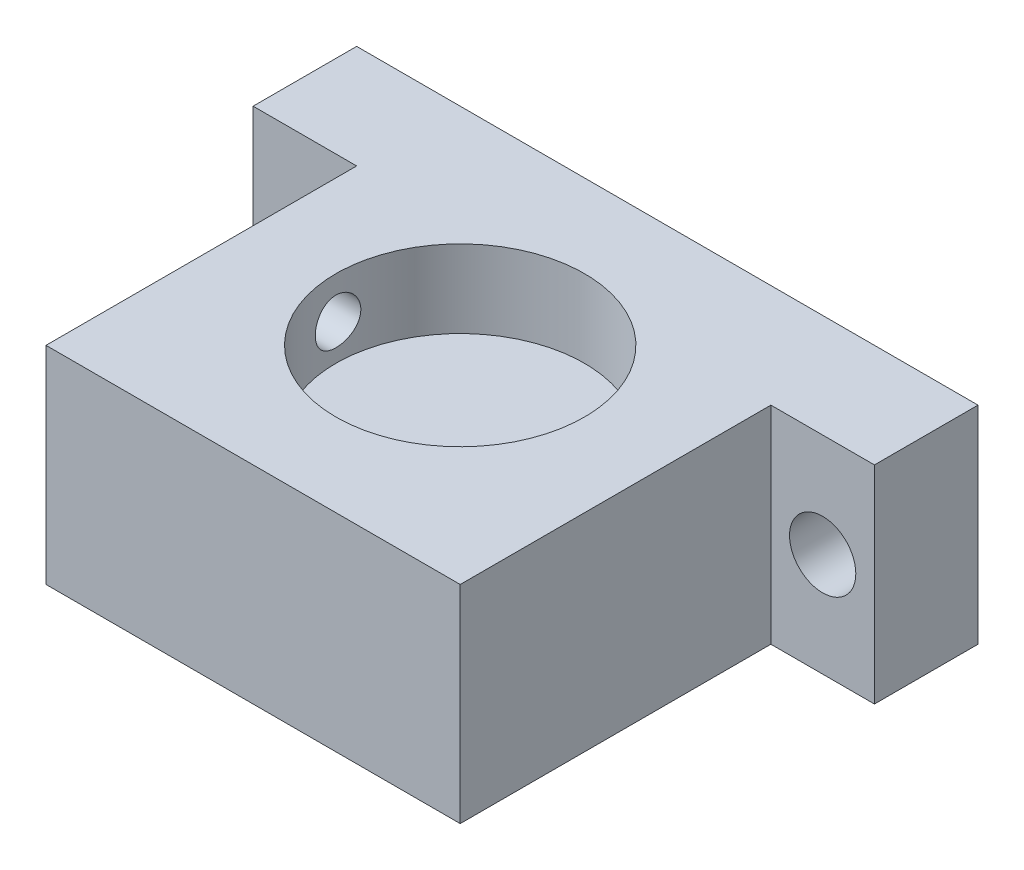
SolidWorks part; units mm, degrees
ref_plane "Front Plane" through (0, 0, 0) normal (0, 0, 1) x (1, 0, 0)
ref_plane "Top Plane" through (0, 0, 0) normal (0, 1, 0) x (1, 0, 0)
ref_plane "Right Plane" through (0, 0, 0) normal (1, 0, 0) x (0, 0, -1)
sketch "Sketch1" plane through (0, 0, 0) normal (0, 1, 0) x (1, 0, 0)
  line L1 (0, 0) -> (20, 0)
  line L2 (0, 0) -> (0, 20)
  line L3 (0, 20) -> (20, 20)
  line L4 (20, 0) -> (20, 20)
  dimension "D1" = 20
  dimension "D2" = 20
extrude "Boss-Extrude1" add sketch "Sketch1" along normal blind 10 contours L4 L3 L2 L1
sketch "Sketch2" plane through (0, 10, 0) normal (0, 1, 0) x (1, 0, 0)
  line L0 (0, 0) -> (0, 20) construction
  line L1 (0, 20) -> (20, 20) construction
  circle A0 centre (10, 10) radius 6
  dimension "D1" = 12
  dimension "D2" = 10
  dimension "D3" = 10
extrude "Cut-Extrude1" cut sketch "Sketch2" against normal blind 3.75
sketch "Sketch5" plane through (0, 0, 0) normal (-1, 0, 0) x (0, 0, 1)
  line L0 (0, 10) -> (-20, 10) construction
  line L1 (-20, 10) -> (-20, 0) construction
  circle A0 centre (-10, 8) radius 1.1
  dimension "D1" = 2.2
  dimension "D2" = 2
  dimension "D3" = 10
extrude "Cut-Extrude3" cut sketch "Sketch5" against normal up to next
sketch "Sketch6" plane through (20, 0, 0) normal (1, 0, 0) x (0, 0, -1)
  line L0 (0, 0) -> (20, 0) construction
  line L1 (20, 10) -> (15, 10)
  line L2 (20, 10) -> (20, 0)
  line L3 (20, 0) -> (15, 0)
  line L4 (15, 10) -> (15, 0)
  dimension "D1" = 5
extrude "Boss-Extrude2" add sketch "Sketch6" along normal blind 5
sketch "Sketch7" plane through (0, 0, -15) normal (0, 0, 1) x (1, 0, 0)
  line L0 (25, 10) -> (20, 10) construction
  line L1 (25, 10) -> (25, 0) construction
  circle A0 centre (22.5, 5) radius 1.6
  point P4 (0, 0)
  point P6 (23.914, 4.7187)
  dimension "D1" = 3.2
  dimension "D2" = 5
  dimension "D3" = 2.5
extrude "Cut-Extrude4" cut sketch "Sketch7" against normal through all
ref_plane "Plane1" through (10, 0, 0) normal (-1, 0, 0) x (0, 0, 1)
mirror "Mirror1" about plane through (10, 0, 0) normal (-1, 0, 0) of "Cut-Extrude4", "Boss-Extrude2"
